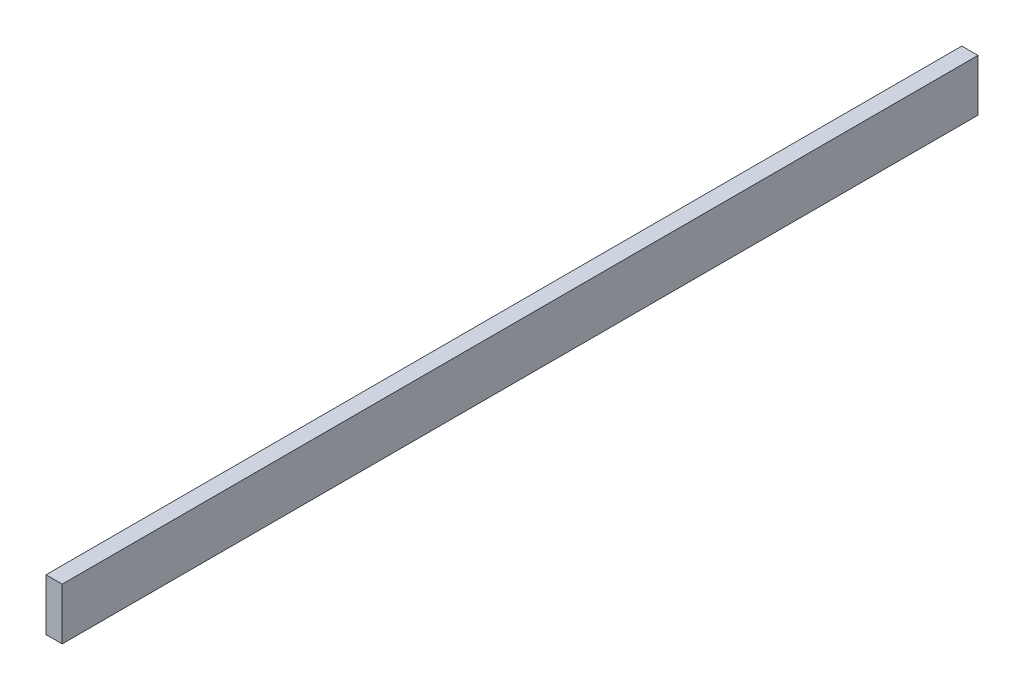
SolidWorks part; units mm, degrees
material "Silicon Rubber"
ref_plane "Front Plane" through (0, 0, 0) normal (0, 0, 1) x (1, 0, 0)
ref_plane "Top Plane" through (0, 0, 0) normal (0, 1, 0) x (1, 0, 0)
ref_plane "Right Plane" through (0, 0, 0) normal (1, 0, 0) x (0, 0, -1)
sketch "Sketch1" plane through (0, 0, 0) normal (1, 0, 0) x (0, 0, -1)
  line L13 (-89.789, -5.08) -> (89.789, -5.08)
  line L14 (-89.789, -5.08) -> (-89.789, 5.08)
  line L15 (-89.789, 5.08) -> (89.789, 5.08)
  line L16 (89.789, -5.08) -> (89.789, 5.08)
  line L17 (-89.789, -5.08) -> (89.789, 5.08) construction
  line L18 (-89.789, 5.08) -> (89.789, -5.08) construction
  point P0 (0, 0)
  dimension "D2" = 179.578
  dimension "D1" = 10.16
extrude "Boss-Extrude1" add sketch "Sketch1" along normal blind 3.175
